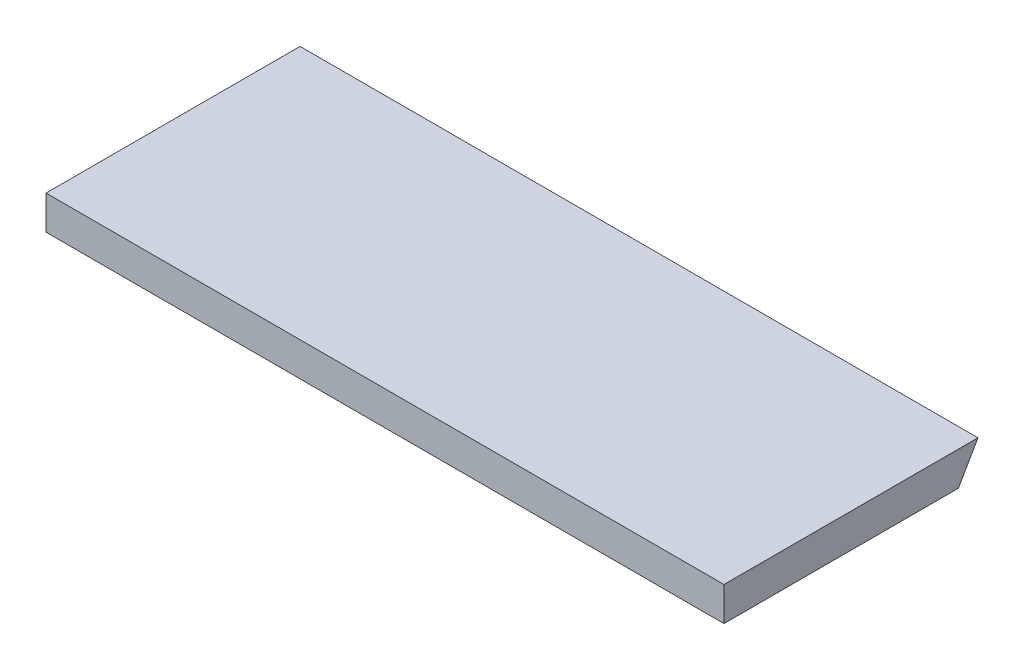
SolidWorks part; units mm, degrees
ref_plane "Front Plane" through (0, 0, 0) normal (0, 0, 1) x (1, 0, 0)
ref_plane "Top Plane" through (0, 0, 0) normal (0, 1, 0) x (1, 0, 0)
ref_plane "Right Plane" through (0, 0, 0) normal (1, 0, 0) x (0, 0, -1)
sketch "Sketch1" plane through (0, 0, 0) normal (1, 0, 0) x (0, 0, -1)
  line L10 (135, 0) -> (135, -12)
  line L16 (12, -12) -> (135, -12)
  line L19 (12, -12) -> (12, 0)
  line L20 (12, 0) -> (135, 0)
extrude "Boss-Extrude1" add sketch "Sketch1" against normal blind 240
extrude "Cut-Extrude1" cut sketch "Sketch2" against normal through all and the other way through all flip side to cut
sketch "Sketch2" plane through (0, -198.2363, -222.1405) normal (1, 0, 0) x (0, 0, -1)
  line L1 (-215.4122, 33.3453) -> (-115.1259, 207.0463)
